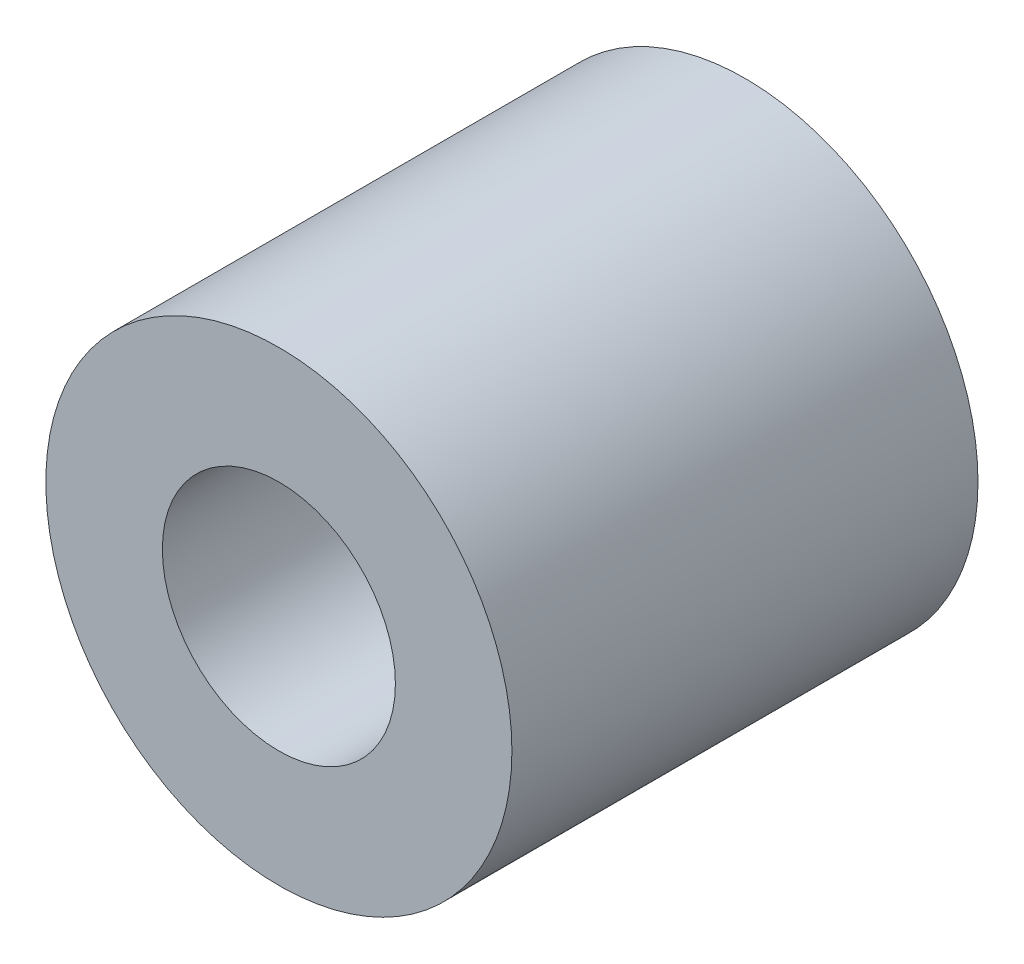
SolidWorks part; units mm, degrees
ref_plane "Front Plane" through (0, 0, 0) normal (0, 0, 1) x (1, 0, 0)
ref_plane "Top Plane" through (0, 0, 0) normal (0, 1, 0) x (1, 0, 0)
ref_plane "Right Plane" through (0, 0, 0) normal (1, 0, 0) x (0, 0, -1)
sketch "Sketch1" plane through (0, 0, 0) normal (0, 0, 1) x (1, 0, 0)
  circle A0 centre (0, 0) radius 2.5
  circle A1 centre (0, 0) radius 5
  dimension "D1" = 5
  dimension "D2" = 10
extrude "Boss-Extrude1" add sketch "Sketch1" along normal blind 10
